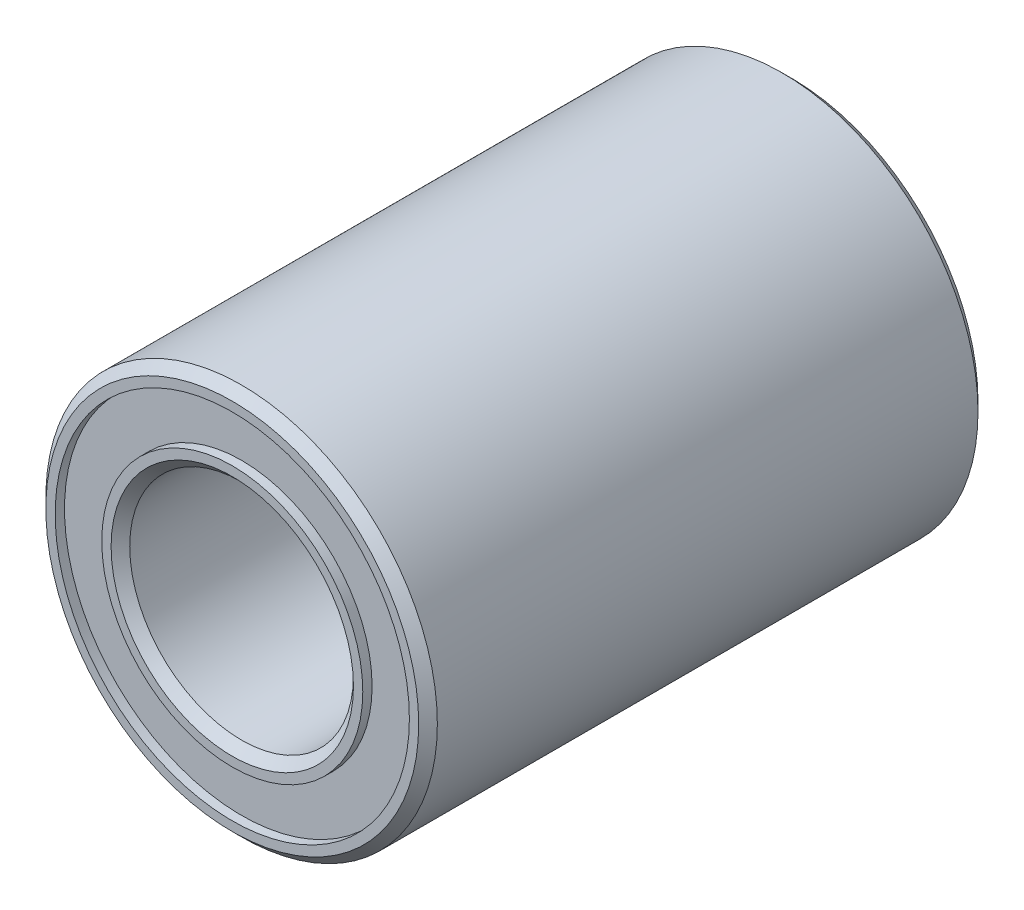
SolidWorks part; units mm, degrees
material "Alloy Steel"
ref_plane "Front Plane" through (0, 0, 0) normal (0, 0, 1) x (1, 0, 0)
ref_plane "Top Plane" through (0, 0, 0) normal (0, 1, 0) x (1, 0, 0)
ref_plane "Right Plane" through (0, 0, 0) normal (1, 0, 0) x (0, 0, -1)
sketch "Sketch1" plane through (0, 0, 0) normal (0, 0, 1) x (1, 0, 0)
  circle A0 centre (0, 0) radius 6
  circle A1 centre (0, 0) radius 10.5
  dimension "D1" = 12
  dimension "D2" = 21
extrude "Boss-Extrude1" add sketch "Sketch1" along normal blind 30
sketch "Sketch2" plane through (0, 0, 30) normal (0, 0, 1) x (1, 0, 0)
  circle A0 centre (0, 0) radius 6 construction
  circle A1 centre (0, 0) radius 10.5
  circle A2 centre (0, 0) radius 10.5 construction
  circle A3 centre (0, 0) radius 6 construction
  circle A4 centre (0, 0) radius 9.5
  circle A5 centre (0, 0) radius 7
  dimension "D1" = 0
  dimension "D2" = 1
  dimension "D3" = 1
extrude "Cut-Extrude1" cut sketch "Sketch2" against normal blind 0.5
sketch "Sketch3" plane through (0, 0, 0) normal (0, 0, -1) x (-1, 0, 0)
  circle A1 centre (0, 0) radius 7
  circle A2 centre (0, 0) radius 7
  circle A3 centre (0, 0) radius 9.5
  circle A4 centre (0, 0) radius 9.5
  dimension "D1" = 0
  dimension "D2" = 0
extrude "Cut-Extrude2" cut sketch "Sketch3" against normal blind 0.5
chamfer "Chamfer1" distance 0.5 angle 45 4 edges at (6, 0, 0) (6, 0, 30) (10.5, 0, 0) (10.5, 0, 30)
